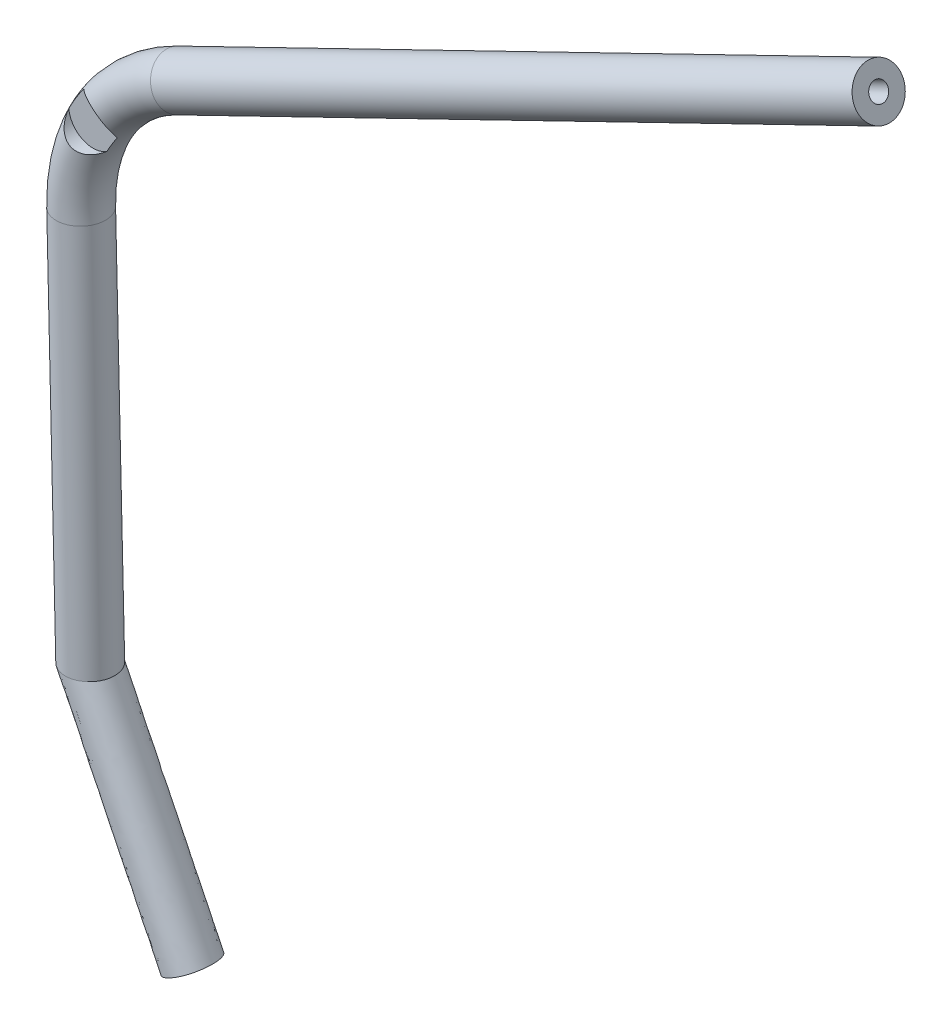
SolidWorks part; units mm, degrees
material "Cast Carbon Steel"
ref_plane "Front Plane" through (0, 0, 0) normal (0, 0, 1) x (1, 0, 0)
ref_plane "Top Plane" through (0, 0, 0) normal (0, 1, 0) x (1, 0, 0)
ref_plane "Right Plane" through (0, 0, 0) normal (1, 0, 0) x (0, 0, -1)
sketch "Sketch4" plane through (0, 0, 0) normal (0, 0, 1) x (1, 0, 0)
  arc A0 (-38.8747, 79.9498) -> (-88.8758, -2.0729) centre (0, 0) ccw
  dimension "D1" = 88.9
  dimension "D2" = 38.8747
  dimension "D3" = 88.8758
sketch "Sketch5" plane through (0, 0, 0) normal (0, 1, 0) x (1, 0, 0)
  circle A0 centre (-88.8758, 0) radius 12.7
  circle A1 centre (-88.8758, 0) radius 4.7625
  dimension "D1" = 25.4
  dimension "D2" = 7.9375
sweep "Sweep1" add profiles "Sketch5" path "Sketch4"
ref_plane "Plane4" through (0, 0, 0) normal (0.8993, 0.4373, 0) x (0, 0, -1)
sketch "Sketch6" plane through (0, 0, 0) normal (0.8993, 0.4373, 0) x (0, 0, -1)
  circle A0 centre (0, 88.8758) radius 12.7
  circle A1 centre (0, 88.8758) radius 4.7625
  circle A2 centre (0, 88.8758) radius 12.7 construction
  dimension "D1" = 7.9375
  dimension "D2" = 9.525
extrude "Boss-Extrude3" add sketch "Sketch6" along normal blind 406.4
ref_plane "Plane5" through (0, 0, 0) normal (0.0233, -0.9997, 0) x (-0.9997, -0.0233, 0)
sketch "Sketch7" plane through (0, 0, 0) normal (0.0233, -0.9997, 0) x (-0.9997, -0.0233, 0)
  circle A0 centre (88.8758, 0) radius 12.7
  circle A1 centre (88.8758, 0) radius 4.7625
  dimension "D1" = 7.9375
  dimension "D2" = 9.525
  dimension "D3" = 88.8758
extrude "Boss-Extrude4" add sketch "Sketch7" along normal blind 203.2
ref_plane "Plane6" through (0, 0, 12.7) normal (0, 0, 1) x (1, 0, 0)
sketch "Sketch8" plane through (0, 0, 12.7) normal (0, 0, 1) x (1, 0, 0)
  line L0 (-76.1551, -1.7762) -> (-101.5482, -2.3685) construction
  line L1 (-33.3106, 68.5067) -> (-44.4176, 91.3495) construction
  circle A0 centre (-76.2699, 46.4942) radius 12.7
  dimension "D1" = 25.4
  dimension "D2" = 48.26
  dimension "D3" = 48.26
extrude "Cut-Extrude1" cut sketch "Sketch8" against normal blind 6.35
ref_plane "Plane7" through (4.7381, -203.1448, 0) normal (0.0233, -0.9997, 0) x (-0.9997, -0.0233, 0)
sketch "Sketch9" plane through (4.7381, -203.1448, 0) normal (0.0233, -0.9997, 0) x (-0.9997, -0.0233, 0)
  circle A0 centre (88.8758, 0) radius 12.7
  circle A1 centre (88.8758, 0) radius 4.7625
  dimension "D1" = 7.9375
  dimension "D2" = 9.525
sketch "Sketch11" plane through (0, 0, 0) normal (0, 0, 1) x (1, 0, 0)
  line L0 (-84.1136, -205.2171) -> (-28.5784, -319.4311)
  line L1 (24.0507, -49.4628) -> (-24.0507, 49.4628) construction
  dimension "D1" = 127
sweep "Sweep2" add profiles "Sketch9" path "Sketch11"
sketch "Sketch16" plane through (0, 0, 0) normal (0, 0, 1) x (1, 0, 0)
  line L0 (-41.2749, -319.7272) -> (-20.5045, -309.6279)
  line L1 (-15.8818, -319.135) -> (-71.417, -204.921) construction
  line L2 (-20.5045, -309.6279) -> (-15.8818, -319.135)
  line L3 (-15.8818, -319.135) -> (-41.2749, -319.7272)
  line L4 (24.0507, -49.4628) -> (-24.0507, 49.4628) construction
extrude "Cut-Extrude2" cut sketch "Sketch16" against normal through all both and the other way through all
